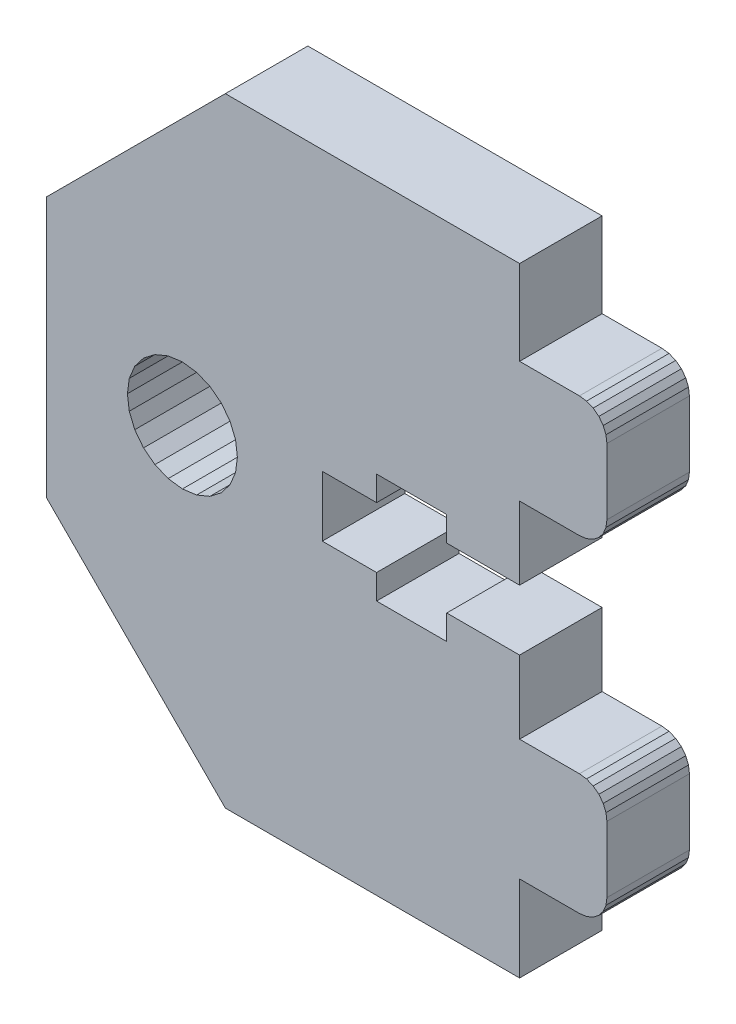
SolidWorks part; units mm, degrees
material "Maple"
ref_plane "Front Plane" through (0, 0, 0) normal (0, 0, 1) x (1, 0, 0)
ref_plane "Top Plane" through (0, 0, 0) normal (0, 1, 0) x (1, 0, 0)
ref_plane "Right Plane" through (0, 0, 0) normal (1, 0, 0) x (0, 0, -1)
sketch "Sketch1" plane through (0, 0, 0) normal (0, 0, 1) x (1, 0, 0)
  line L5305 (57.5215, -355.4629) -> (44.5215, -368.4629)
  line L5306 (78.9215, -400.4629) -> (78.9215, -394.2229)
  line L5307 (78.9215, -355.4629) -> (57.5215, -355.4629)
  line L5308 (44.5215, -387.4229) -> (44.5215, -368.4629)
  line L5309 (44.5215, -387.4229) -> (57.5215, -400.4629)
  line L5310 (85.2715, -368.4229) -> (85.2715, -363.6229)
  line L5311 (78.9215, -370.4229) -> (83.2715, -370.4229)
  line L5312 (83.2715, -361.6229) -> (78.9215, -361.6229)
  line L5313 (83.2715, -370.4229) -> (83.7891, -370.3548)
  line L5314 (84.2715, -370.155) -> (84.6857, -369.8371)
  line L5315 (83.7891, -370.3548) -> (84.2715, -370.155)
  line L5316 (64.5715, -380.1229) -> (64.5715, -375.7229)
  line L5317 (73.6215, -373.9229) -> (73.6215, -375.7229)
  line L5318 (68.5215, -375.7229) -> (68.5215, -373.9229)
  line L5319 (84.6857, -386.0087) -> (85.0035, -386.4229)
  line L5320 (68.5215, -381.9229) -> (68.5215, -380.1229)
  line L5321 (85.2715, -392.2229) -> (85.2715, -387.4229)
  line L5322 (85.0035, -393.2229) -> (85.2033, -392.7405)
  line L5323 (84.6857, -393.6371) -> (85.0035, -393.2229)
  line L5324 (68.5215, -380.1229) -> (64.5715, -380.1229)
  line L5325 (84.2715, -393.955) -> (84.6857, -393.6371)
  line L5326 (83.7891, -394.1548) -> (84.2715, -393.955)
  line L5327 (84.2715, -385.6909) -> (84.6857, -386.0087)
  line L5328 (85.0035, -386.4229) -> (85.2033, -386.9053)
  line L5329 (83.7891, -385.4911) -> (84.2715, -385.6909)
  line L5330 (83.2715, -385.4229) -> (83.7891, -385.4911)
  line L5331 (83.2715, -385.4229) -> (78.9215, -385.4229)
  line L5332 (85.2033, -392.7405) -> (85.2715, -392.2229)
  line L5333 (83.2715, -394.2229) -> (83.7891, -394.1548)
  line L5334 (73.6215, -380.1229) -> (73.6215, -381.9229)
  line L5335 (64.5715, -375.7229) -> (68.5215, -375.7229)
  line L5336 (78.9215, -394.2229) -> (83.2715, -394.2229)
  line L5337 (68.5215, -373.9229) -> (73.6215, -373.9229)
  line L5338 (85.2033, -386.9053) -> (85.2715, -387.4229)
  line L5339 (83.7891, -361.6911) -> (84.2715, -361.8909)
  line L5340 (73.6215, -381.9229) -> (68.5215, -381.9229)
  line L5341 (85.2033, -368.9406) -> (85.2715, -368.4229)
  line L5342 (84.2715, -361.8909) -> (84.6857, -362.2087)
  line L5343 (84.6857, -362.2087) -> (85.0035, -362.6229)
  line L5344 (85.0035, -362.6229) -> (85.2033, -363.1053)
  line L5345 (84.6857, -369.8371) -> (85.0035, -369.4229)
  line L5346 (85.0035, -369.4229) -> (85.2033, -368.9406)
  line L5347 (85.2033, -363.1053) -> (85.2715, -363.6229)
  line L5348 (78.9215, -380.1229) -> (73.6215, -380.1229)
  line L5349 (73.6215, -375.7229) -> (78.9215, -375.7229)
  line L5350 (83.2715, -361.6229) -> (83.7891, -361.6911)
  line L5351 (78.9215, -375.7229) -> (78.9215, -370.4229)
  line L5352 (78.9215, -385.4229) -> (78.9215, -380.1229)
  line L5353 (78.9215, -361.6229) -> (78.9215, -355.4629)
  line L5354 (50.3987, -377.9229) -> (50.535, -378.9582)
  line L5355 (54.3987, -373.9229) -> (53.3635, -374.0592)
  line L5356 (58.2625, -378.9582) -> (58.3987, -377.9229)
  line L5357 (57.8629, -379.9229) -> (58.2625, -378.9582)
  line L5358 (50.9346, -379.9229) -> (51.5703, -380.7513)
  line L5359 (58.2625, -376.8876) -> (57.8629, -375.9229)
  line L5360 (53.3635, -374.0592) -> (52.3987, -374.4588)
  line L5361 (53.3635, -381.7866) -> (54.3987, -381.9229)
  line L5362 (55.434, -374.0592) -> (54.3987, -373.9229)
  line L5363 (51.5703, -375.0945) -> (50.9346, -375.9229)
  line L5364 (57.8629, -375.9229) -> (57.2272, -375.0945)
  line L5365 (51.5703, -380.7513) -> (52.3987, -381.387)
  line L5366 (50.9346, -375.9229) -> (50.535, -376.8876)
  line L5367 (50.535, -376.8876) -> (50.3987, -377.9229)
  line L5368 (56.3987, -374.4588) -> (55.434, -374.0592)
  line L5369 (57.2272, -375.0945) -> (56.3987, -374.4588)
  line L5370 (52.3987, -381.387) -> (53.3635, -381.7866)
  line L5371 (57.2272, -380.7513) -> (57.8629, -379.9229)
  line L5372 (52.3987, -374.4588) -> (51.5703, -375.0945)
  line L5373 (55.434, -381.7866) -> (56.3987, -381.387)
  line L5374 (56.3987, -381.387) -> (57.2272, -380.7513)
  line L5375 (54.3987, -381.9229) -> (55.434, -381.7866)
  line L5376 (50.535, -378.9582) -> (50.9346, -379.9229)
  line L5377 (58.3987, -377.9229) -> (58.2625, -376.8876)
  line L8416 (57.5215, -400.4629) -> (78.9215, -400.4629)
  line L9303 (67.733, -389.5532) -> (67.733, -385.2453)
  line L9304 (67.733, -385.2453) -> (67.733, -389.5532)
  line L9305 (67.733, -389.5532) -> (69.8622, -389.5532)
  line L9306 (69.8622, -389.5532) -> (67.733, -389.5532)
extrude "Boss-Extrude1" add sketch "Sketch1" along normal blind 6
